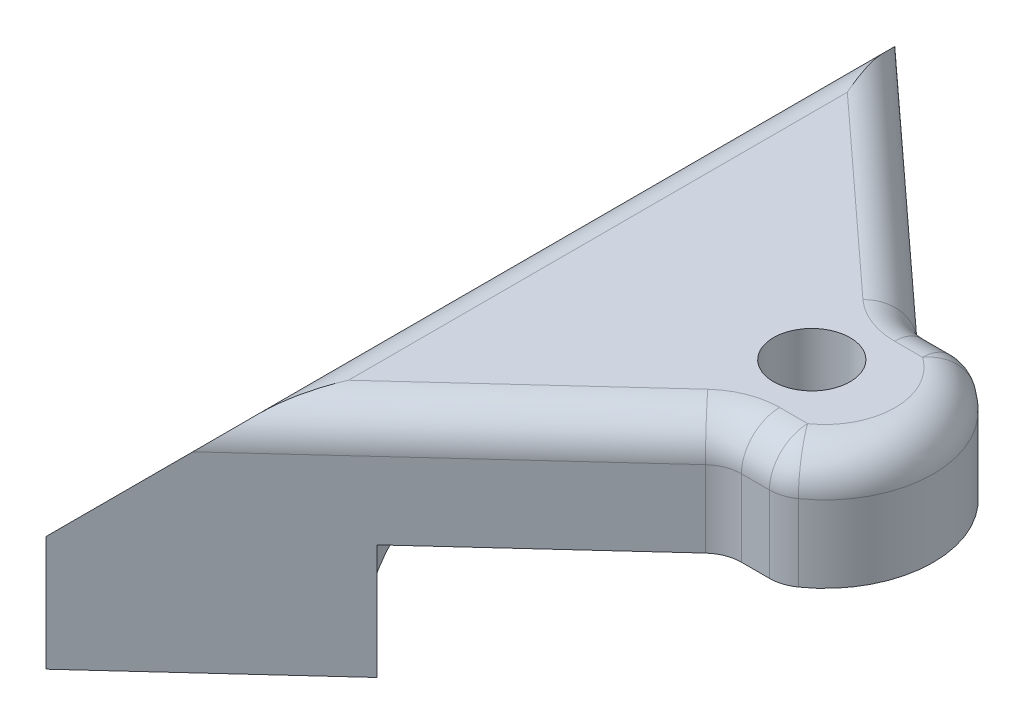
SolidWorks part; units mm, degrees
ref_plane "Front Plane" through (0, 0, 0) normal (0, 0, 1) x (1, 0, 0)
ref_plane "Top Plane" through (0, 0, 0) normal (0, 1, 0) x (1, 0, 0)
ref_plane "Right Plane" through (0, 0, 0) normal (1, 0, 0) x (0, 0, -1)
sketch "Sketch1" plane through (0, 0, 0) normal (0, 1, 0) x (1, 0, 0)
  line L3 (-6, -26.8424) -> (40.3636, 15.6576)
  line L4 (40.3636, 40.6576) -> (-6, 83.1576)
  line L5 (-6, 83.1576) -> (-6, -26.8424) construction
  line L6 (40.3636, 28.1576) -> (-6, 28.1576) construction
  line L7 (-6, 83.1576) -> (-6, -26.8424)
  line L8 (40.3636, 40.6576) -> (40.3636, 15.6576) construction
  line L9 (40.3636, 40.6576) -> (47.3636, 40.6576)
  line L11 (47.3636, 15.6576) -> (40.3636, 15.6576)
  arc A0 (47.3636, 40.6576) -> (47.3636, 15.6576) centre (40.697, 28.1576) cw
  dimension "D1" = 110
  dimension "D2" = 7
extrude "Boss-Extrude1" add sketch "Sketch1" along normal blind 15
sketch "Sketch2" plane through (0, 0, 0) normal (0, -1, 0) x (1, 0, 0)
  line L0 (-6, -28.1576) -> (47.5, -28.1576) construction
  line L2 (30.5, -19.6576) -> (30.5, -36.6576)
  line L4 (47.5, -19.6576) -> (47.5, -36.6576)
  line L7 (30.5, -19.6576) -> (47.5, -19.6576)
  line L8 (30.5, -36.6576) -> (47.5, -36.6576)
  line L9 (30.5, -24.1576) -> (9.5, -24.1576)
  line L10 (9.5, -24.1576) -> (9.5, -32.1576)
  line L11 (9.5, -32.1576) -> (30.5, -32.1576)
  line L13 (39, -19.6576) -> (39, -36.6576) construction
  line L14 (-6, -83.1576) -> (-6, 26.8424) construction
  point P12 (9.5, -28.1576)
  dimension "D1" = 45
  dimension "D2" = 21
  dimension "D3" = 17
  dimension "D4" = 17
  dimension "D5" = 8
extrude "Cut-Extrude2" cut sketch "Sketch2" against normal blind 6 contours L10 L11 L2 L9 | L2 L8 L4 L7
sketch "Sketch3" plane through (0, 6, 0) normal (0, 1, 0) x (-1, 0, 0)
  line L0 (-47.5, -19.6576) -> (-30.5, -36.6576) construction
  line L1 (-30.5, -19.6576) -> (-47.5, -36.6576) construction
  circle A0 centre (-39, -28.1576) radius 5
  point P10 (-39, -28.1576)
  dimension "D1" = 10
extrude "Cut-Extrude3" cut sketch "Sketch3" along normal through all
sketch "Sketch6" plane through (0, 0, 0) normal (0, -1, 0) x (1, 0, 0)
  line L2 (-6, 26.8424) -> (39, 26.8424) construction
  line L3 (39, 26.8424) -> (39, -83.1576) construction
  line L4 (39, -83.1576) -> (-6, -83.1576) construction
  line L5 (-6, 26.8424) -> (-6, -83.1576)
  line L6 (-6, 26.8424) -> (16.5639, 6.1589)
  line L7 (-6, 26.8424) -> (40.3636, -15.6576) construction
  line L8 (-6, -83.1576) -> (16.5639, -62.474)
  line L9 (40.3636, -40.6576) -> (-6, -83.1576) construction
  arc A0 (16.5639, 6.1589) -> (16.5639, -62.474) centre (39, -28.1576) ccw
  dimension "D1" = 45
  dimension "D2" = 41
extrude "Boss-Extrude3" add sketch "Sketch6" along normal blind 15
sketch "Sketch5" plane through (-6, 0, 0) normal (-1, 0, 0) x (0, 0, 1)
  line L0 (-83.1576, -8) -> (26.8424, -8) construction
  line L1 (-83.1576, 0) -> (26.8424, 0) construction
  line L2 (-83.1576, 15) -> (-83.1576, -15) construction
  line L3 (26.8424, 15) -> (26.8424, -15) construction
  line L4 (-53.1576, -11.5) -> (-3.1576, -11.5) construction
  line L5 (-28.1576, -11.5) -> (-28.1576, 15) construction
  line L6 (26.8424, -15) -> (-83.1576, -15) construction
  line L9 (-83.1576, 15) -> (26.8424, 15) construction
  line L10 (-83.1576, 15) -> (-83.1576, -15) construction
  line L11 (26.8424, 15) -> (26.8424, -15) construction
  circle A0 centre (-53.1576, -8) radius 3.5
  circle A1 centre (-3.1576, -8) radius 3.5
  point P24 (-53.1576, -6.5915)
  dimension "D1" = 7
  dimension "D2" = 8
  dimension "D3" = 50
  dimension "D4" = 15
extrude "Boss-Extrude4" add sketch "Sketch5" along normal blind 4
chamfer "Chamfer1" distance 15 angle 45 1 edges at (-6, 15, -28.1576)
fillet "Fillet1" radius 5 10 edges at (54.8636, 15, -28.1576) (40.3636, 7.5, -15.6576) (40.3636, 7.5, -40.6576) (47.3636, 7.5, -40.6576) (47.3636, 7.5, -15.6576) (43.8636, 15, -40.6576) (24.6818, 15, -55.0326) (43.8636, 15, -15.6576) (24.6818, 15, -1.2826) (9, 15, -28.1576)
